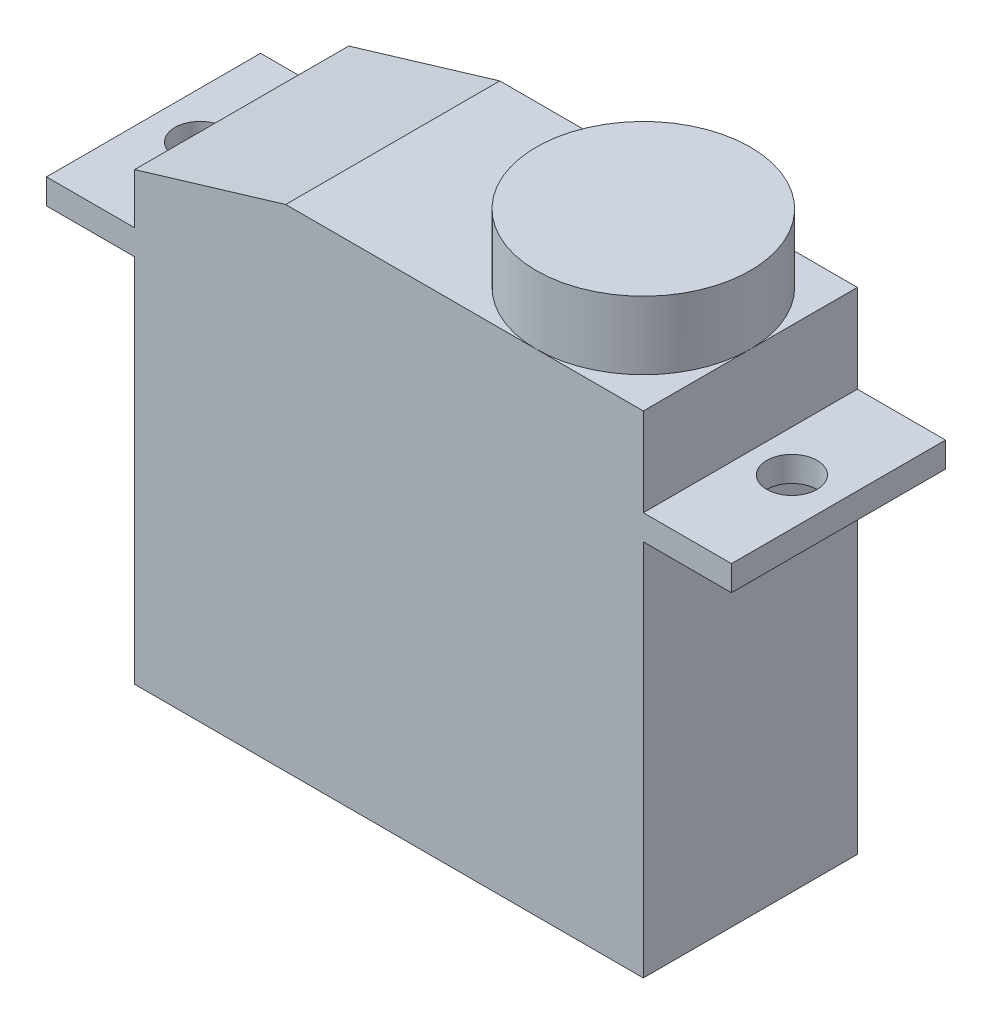
SolidWorks part; units mm, degrees
ref_plane "Plan de face" through (0, 0, 0) normal (0, 0, 1) x (1, 0, 0)
ref_plane "Plan de dessus" through (0, 0, 0) normal (0, 1, 0) x (1, 0, 0)
ref_plane "Plan de droite" through (0, 0, 0) normal (1, 0, 0) x (0, 0, -1)
sketch "Sketch1" plane through (0, 0, 0) normal (0, 0, 1) x (1, 0, 0)
  line L0 (0, 0) -> (-20.2, 0)
  line L1 (-20.2, 0) -> (-20.2, 14.7)
  line L2 (-20.2, 14.7) -> (-23.7, 14.7)
  line L3 (-23.7, 14.7) -> (-23.7, 15.7)
  line L4 (-23.7, 15.7) -> (-20.2, 15.7)
  line L5 (-20.2, 15.7) -> (-20.2, 17.7)
  line L6 (-20.2, 17.7) -> (-14.2, 19.5)
  line L7 (-14.2, 19.5) -> (0, 19.5)
  line L8 (0, 0) -> (0, 15)
  line L9 (0, 15) -> (3.5, 15)
  line L10 (3.5, 15) -> (3.5, 16)
  line L11 (3.5, 16) -> (0, 16)
  line L12 (0, 16) -> (0, 19.5)
  dimension "D1" = 20.2
  dimension "D2" = 19.5
  dimension "D3" = 14.7
  dimension "D4" = 1
  dimension "D5" = 2
  dimension "D6" = 3.5
  dimension "D7" = 6
  dimension "D8" = 1
  dimension "D9" = 3.5
  dimension "D10" = 3.5
  dimension "D11" = 3.5
extrude "Boss-Extrude1" add sketch "Sketch1" along normal blind 8.5
sketch "Sketch2" plane through (0, 19.5, 0) normal (0, 1, 0) x (1, 0, 0)
  line L0 (0, -8.5) -> (0, 0) construction
  line L1 (0, 0) -> (-14.2, 0) construction
  circle A0 centre (-4.25, -4.25) radius 4.25
  dimension "D1" = 8.5
  dimension "D2" = 4.25
  dimension "D3" = 4.25
extrude "Boss-Extrude2" add sketch "Sketch2" along normal blind 2.7 contours A0
sketch "Sketch3" plane through (0, 15.7, 0) normal (0, 1, 0) x (1, 0, 0)
  line L0 (-20.2, -8.5) -> (-20.2, 0) construction
  line L3 (-20.2, 0) -> (-23.7, 0) construction
  line L4 (3.5, 0) -> (0, 0) construction
  circle A0 centre (-21.85, -4.25) radius 1
  circle A1 centre (1.65, -4.25) radius 1
  dimension "D1" = 2
  dimension "D2" = 2
  dimension "D3" = 23.5
  dimension "D4" = 1.65
  dimension "D5" = 4.25
  dimension "D6" = 4.25
extrude "Cut-Extrude1" cut sketch "Sketch3" against normal through all and the other way through all
